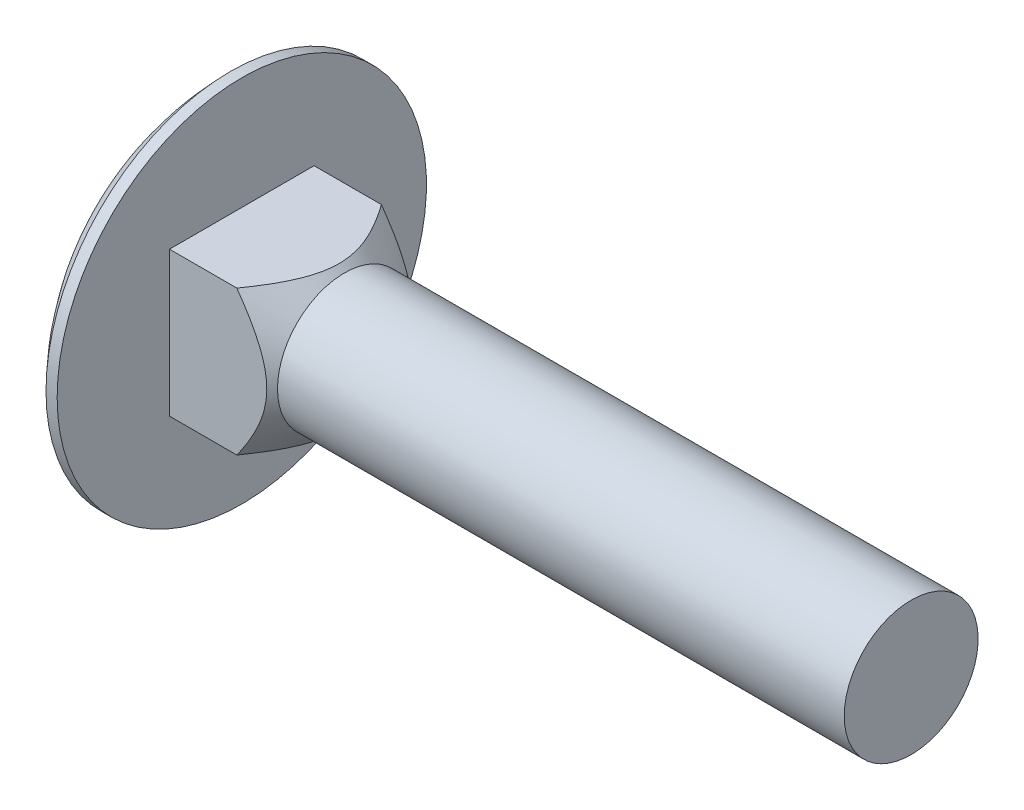
SolidWorks part; units mm, degrees
material "AISI 1035 Сталь (SS)"
ref_plane "Спереди" through (0, 0, 0) normal (0, 0, 1) x (1, 0, 0)
ref_plane "Сверху" through (0, 0, 0) normal (0, 1, 0) x (1, 0, 0)
ref_plane "Справа" through (0, 0, 0) normal (1, 0, 0) x (0, 0, -1)
sketch "Эскиз1" plane through (0, 0, 0) normal (0, 0, 1) x (1, 0, 0)
  line L0 (30, 0) -> (-3.88, 0)
  line L1 (-946.3906, 0) -> (47987.4811, 0) construction
  line L2 (30, 0) -> (30, 3)
  line L3 (30, 3) -> (0, 3)
  line L4 (0, 3) -> (0, 8.275)
  line L5 (0, 8.275) -> (-0.5, 8.275)
  arc A0 (-0.5, 8.275) -> (-3.88, 0) centre (7.9395, 0) ccw
  dimension "D1" = 30
  dimension "D2" = 16.55
  dimension "D3" = 6
  dimension "D4" = 3.88
  dimension "D5" = 0.5
revolve "Повернуть1" add sketch "Эскиз1" angle 360 about L1
cosmetic thread "Условное изображение резьбы1" parameters "D2"=4.891
cosmetic thread "Условное изображение резьбы2" [suppressed] parameters "D1"=20, "D2"=4.891
sketch "Эскиз2" plane through (0, 0, 0) normal (1, 0, 0) x (0, 0, -1)
  line L1 (-3.24, 3.24) -> (3.24, 3.24)
  line L2 (-3.24, 3.24) -> (-3.24, -3.24)
  line L3 (-3.24, -3.24) -> (3.24, -3.24)
  line L4 (3.24, 3.24) -> (3.24, -3.24)
  line L5 (-3.24, 3.24) -> (3.24, -3.24) construction
  line L6 (-3.24, -3.24) -> (3.24, 3.24) construction
  point P0 (0, 0)
  dimension "D1" = 6.48
extrude "Бобышка-Вытянуть1" add sketch "Эскиз2" along normal blind 4.6
ref_plane "Плоскость1" through (0, 0, 0) normal (0, -0.7071, 0.7071) x (-1, 0, 0)
sketch "Эскиз3" plane through (0, 0, 0) normal (0, -0.7071, 0.7071) x (-1, 0, 0)
  line L0 (-1000, 0) -> (49000, 0) construction
  line L1 (-4.6, 3) -> (-2.0179, 5.5821)
  line L2 (-2.0179, 5.5821) -> (-7.1821, 5.5821)
  line L3 (-7.1821, 5.5821) -> (-4.6, 3)
  line L4 (-4.6, 3) -> (-30, 3) construction
  line L6 (-4.6, 0) -> (-4.6, 4.5821) construction
  line L7 (-4.6, 4.5821) -> (0, 4.5821) construction
  dimension "D1" = 45
  dimension "D2" = 1
revolve "Повернуть2" add sketch "Эскиз3" angle 360 about L0
combine bodies "Соединить1" operation type subtract main body 104 bodies to subtract 105
